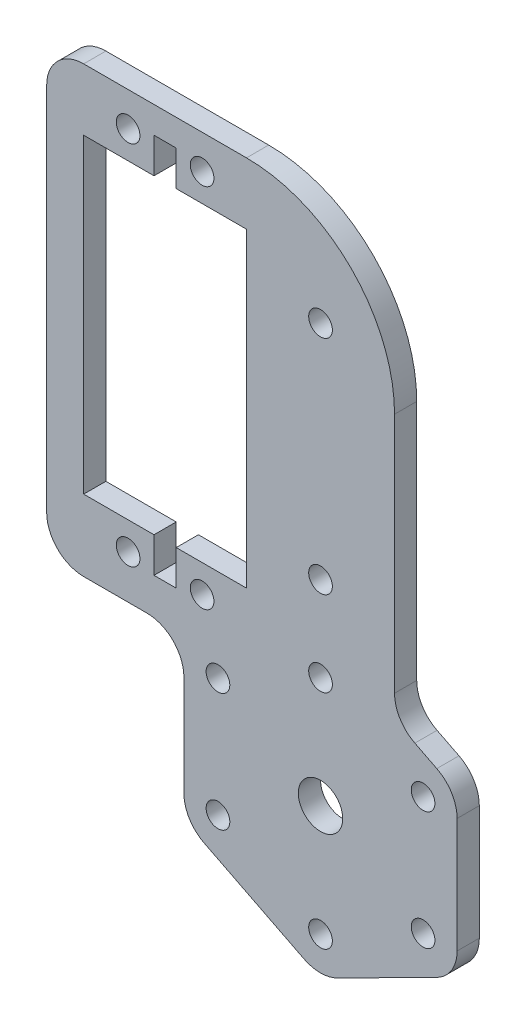
SolidWorks part; units mm, degrees
ref_plane "Plano frontal" through (0, 0, 0) normal (0, 0, 1) x (1, 0, 0)
ref_plane "Plano superior" through (0, 0, 0) normal (0, 1, 0) x (1, 0, 0)
ref_plane "Plano direito" through (0, 0, 0) normal (1, 0, 0) x (0, 0, -1)
ref_plane "Plano1" through (0, 0, -13) normal (0, 0, -1) x (-1, 0, 0)
sketch "Esboço1" plane through (0, 0, -13) normal (0, 0, -1) x (-1, 0, 0)
  line L0 (-1.5, -21) -> (-11, -21)
  line L1 (-11, -21) -> (-11, 21)
  line L2 (-11, 21) -> (-1.5, 21)
  line L3 (-1.5, 21) -> (-1.5, 25.75)
  line L4 (-1.5, 25.75) -> (1.5, 25.75)
  line L5 (1.5, 25.75) -> (1.5, 21)
  line L6 (1.5, 21) -> (11, 21)
  line L7 (11, 21) -> (11, -21)
  line L8 (11, -21) -> (1.5, -21)
  line L9 (1.5, -21) -> (1.5, -25.75)
  line L10 (1.5, -25.75) -> (-1.5, -25.75)
  line L11 (-1.5, -25.75) -> (-1.5, -21)
  line L12 (11, 29.35) -> (-11, 29.35)
  line L13 (-31, 9.35) -> (-31, -23.299)
  line L14 (-33.7455, -27.7618) -> (-36.711, -29.26)
  line L15 (-39.4564, -33.7228) -> (-39.4564, -49.2307)
  line L16 (-36.711, -53.6935) -> (-23.2545, -60.4914)
  line L17 (-18.7455, -60.4914) -> (-5.289, -53.6935)
  line L18 (-2.5436, -49.2307) -> (-2.5436, -35.6469)
  line L19 (2.4564, -30.6469) -> (11, -30.6469)
  line L20 (16, -25.6469) -> (16, 24.35)
  line L21 (-34.8564, -33.4767) -> (-7.1436, -49.4767) construction
  line L22 (-21, -26.4767) -> (-21, -56.4767) construction
  line L23 (-11, 21) -> (11, -21) construction
  line L24 (5, 24.75) -> (-5, -24.75) construction
  arc A0 (-11, 29.35) -> (-31, 9.35) centre (-11, 9.35) ccw
  arc A1 (-31, -23.299) -> (-33.7455, -27.7618) centre (-36, -23.299) cw
  arc A2 (-36.711, -29.26) -> (-39.4564, -33.7228) centre (-34.4564, -33.7228) ccw
  arc A3 (-39.4564, -49.2307) -> (-36.711, -53.6935) centre (-34.4564, -49.2307) ccw
  arc A4 (-23.2545, -60.4914) -> (-18.7455, -60.4914) centre (-21, -56.0286) ccw
  arc A5 (-5.289, -53.6935) -> (-2.5436, -49.2307) centre (-7.5436, -49.2307) ccw
  arc A6 (-2.5436, -35.6469) -> (2.4564, -30.6469) centre (2.4564, -35.6469) cw
  arc A7 (11, -30.6469) -> (16, -25.6469) centre (11, -25.6469) ccw
  arc A8 (16, 24.35) -> (11, 29.35) centre (11, 24.35) ccw
  circle A9 centre (-5, -24.75) radius 1.6
  circle A10 centre (-5, 24.75) radius 1.6
  circle A11 centre (5, -24.75) radius 1.6
  circle A12 centre (5, 24.75) radius 1.6
  circle A13 centre (-21, 15) radius 1.6
  circle A14 centre (-21, -15) radius 1.6
  circle A15 centre (-7.1436, -33.4767) radius 1.6
  circle A16 centre (-7.1436, -49.4767) radius 1.6
  circle A17 centre (-21, -26.4767) radius 1.6
  circle A18 centre (-21, -56.4767) radius 1.6
  circle A19 centre (-21, -41.4767) radius 3
  circle A20 centre (-34.8564, -33.4767) radius 1.6
  circle A21 centre (-34.8564, -49.4767) radius 1.6
  point P65 (0, 0)
  point P66 (0, 0)
  point P67 (0, 0)
  point P68 (0, 0)
  point P69 (0, 0)
  point P70 (0, 0)
  point P71 (84.2332, -41.0726)
  point P72 (0, 0)
  point P73 (0, -25.75)
  point P74 (0, 25.75)
  point P75 (0, 0)
  point P76 (0, 0)
  dimension "D2" = 16
  dimension "D3" = 3.2
  dimension "D4" = 6
  dimension "D5" = 30
  dimension "D6" = 10
  dimension "D7" = 49.5
  dimension "D17" = 20
  dimension "D18" = 5
  dimension "D19" = 4.6
  dimension "D27" = 4.6
  dimension "D28" = 4.6
  dimension "D29" = 4.6
  dimension "D1" = 27.7128
  dimension "D8" = 22
  dimension "D9" = 42
  dimension "D10" = 41.4767
  dimension "D11" = 21
  dimension "D12" = 49.5
  dimension "D13" = 4.75
  dimension "D14" = 3
  dimension "D15" = 15
  dimension "D16" = 30
  dimension "D20" = 5
  dimension "D21" = 20
  dimension "D22" = 5.8969
  dimension "D23" = 4.6
  dimension "D24" = 4.6
  dimension "D25" = 4.6
  dimension "D26" = 4.6
  dimension "D30" = 3.3224
extrude "Ressalto-extrusão1" add sketch "Esboço1" against normal blind 3
